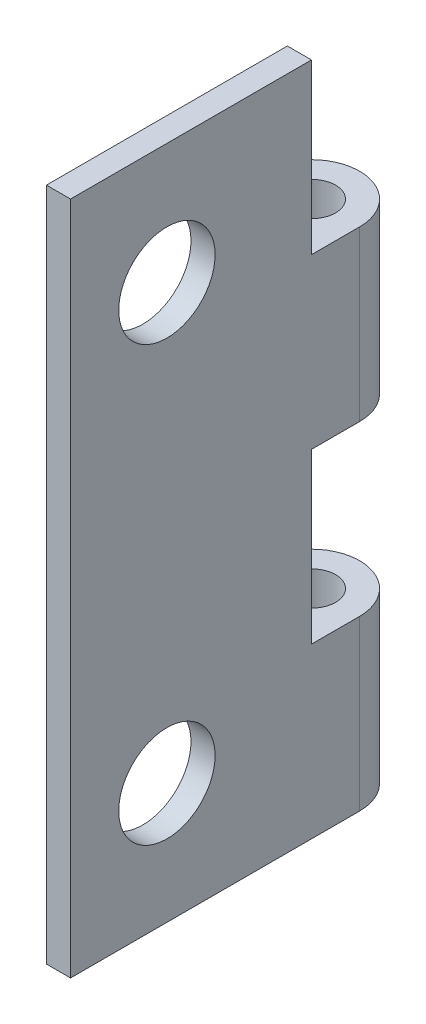
SolidWorks part; units mm, degrees
ref_plane "Front Plane" through (0, 0, 0) normal (0, 0, 1) x (1, 0, 0)
ref_plane "Top Plane" through (0, 0, 0) normal (0, 1, 0) x (1, 0, 0)
ref_plane "Right Plane" through (0, 0, 0) normal (1, 0, 0) x (0, 0, -1)
sketch "Sketch1" plane through (0, 0, 0) normal (0, 1, 0) x (1, 0, 0)
  line L0 (-0.7333, 3) -> (-0.7333, -9)
  line L5 (-0.7333, -9) -> (0.2667, -9)
  line L6 (0.2667, -9) -> (0.2667, 3)
  circle A0 centre (-1.7333, 3) radius 1
  arc A1 (0.2667, 3) -> (-0.7333, 1.2679) centre (-1.7333, 3) ccw
  point P5 (0, 0)
  point P9 (0, 0)
  point P10 (0, 0)
  point P11 (0, -0.0869)
  point P12 (0, 0)
  point P13 (1, 3)
  point P14 (0, 0)
  point P15 (0, 0)
  point P16 (0, 0)
  point P17 (0, 0)
  point P19 (0, 0)
  point P20 (1, -3.4151)
  point P21 (1, 0)
  point P22 (1, 3)
  point P23 (0, 0)
  point P24 (0, 0)
  point P25 (-0.1666, 3)
  point P26 (0, 0)
  point P27 (0, 0)
  dimension "D3" = 12
  dimension "D1" = 2
  dimension "D2" = 1
extrude "Boss-Extrude1" add sketch "Sketch1" along normal blind 28
sketch "Sketch2" plane through (0.2667, 0, 0) normal (1, 0, 0) x (0, 0, -1)
  line L0 (-9, 28) -> (3, 28) construction
  line L1 (1, 28) -> (6.7069, 28)
  line L2 (1, 28) -> (1, 21)
  line L3 (1, 21) -> (6.7069, 21)
  line L4 (6.7069, 28) -> (6.7069, 21)
  line L5 (-9, 28) -> (-9, 0) construction
  line L7 (1, 14) -> (6.7069, 14)
  line L8 (1, 14) -> (1, 7)
  line L9 (1, 7) -> (6.7069, 7)
  line L10 (6.7069, 14) -> (6.7069, 7)
  dimension "D1" = 7
  dimension "D2" = 10
  dimension "D3" = 7
  dimension "D4" = 7
  dimension "D5" = 10
extrude "Cut-Extrude1" cut sketch "Sketch2" against normal through all
sketch "Sketch3" plane through (0.2667, 0, 0) normal (1, 0, 0) x (0, 0, -1)
  line L0 (-9, 28) -> (-9, 0) construction
  line L1 (-9, 28) -> (1, 28) construction
  line L2 (-9, 0) -> (3, 0) construction
  circle A0 centre (-5, 23) radius 2
  circle A1 centre (-5, 5) radius 2
  dimension "D2" = 4
  dimension "D6" = 4
  dimension "D1" = 4
  dimension "D3" = 5
  dimension "D4" = 4
  dimension "D5" = 5
  dimension "D7" = 18
extrude "Cut-Extrude2" cut sketch "Sketch3" against normal through all
